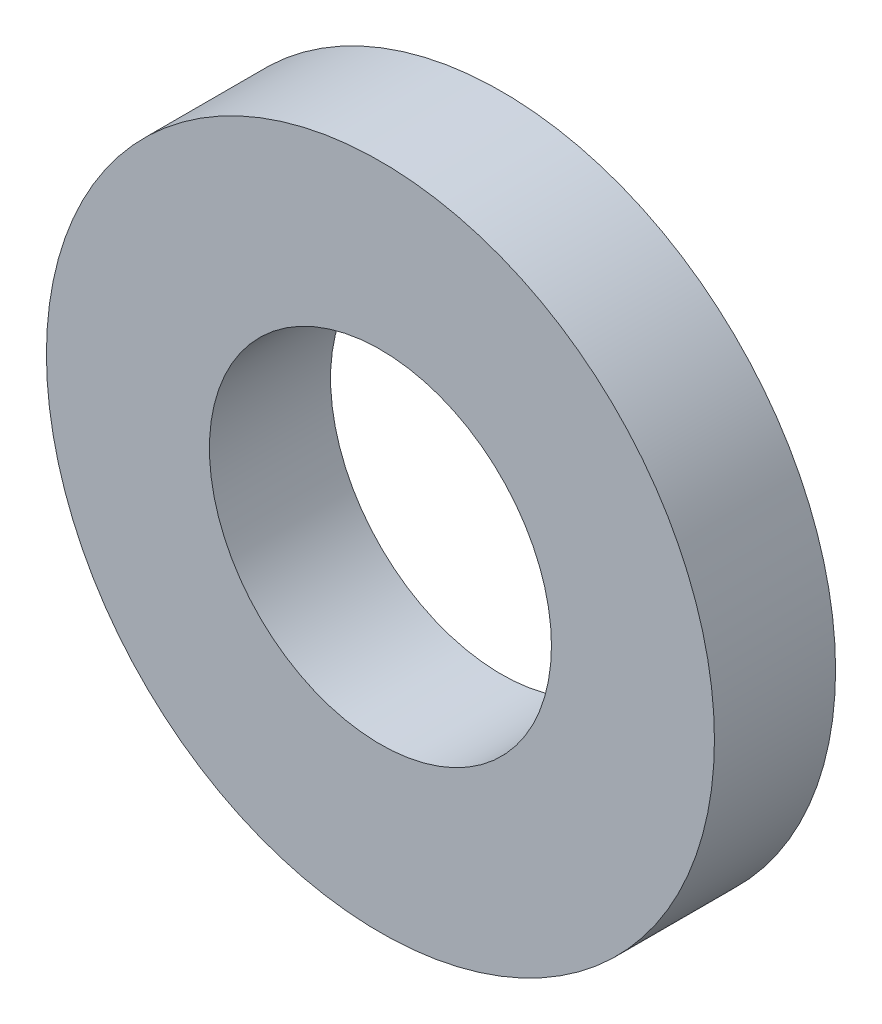
SolidWorks part; units mm, degrees
ref_plane "Front Plane" through (0, 0, 0) normal (0, 0, 1) x (1, 0, 0)
ref_plane "Top Plane" through (0, 0, 0) normal (0, 1, 0) x (1, 0, 0)
ref_plane "Right Plane" through (0, 0, 0) normal (1, 0, 0) x (0, 0, -1)
sketch "Sketch1" plane through (0, 0, 0) normal (0, 0, 1) x (1, 0, 0)
  circle A0 centre (0, 0) radius 2.4384
  circle A1 centre (0, 0) radius 4.7625
  dimension "ID" = 4.8768
  dimension "OD" = 9.525
extrude "Extrude1" add sketch "Sketch1" against normal blind 1.7272
